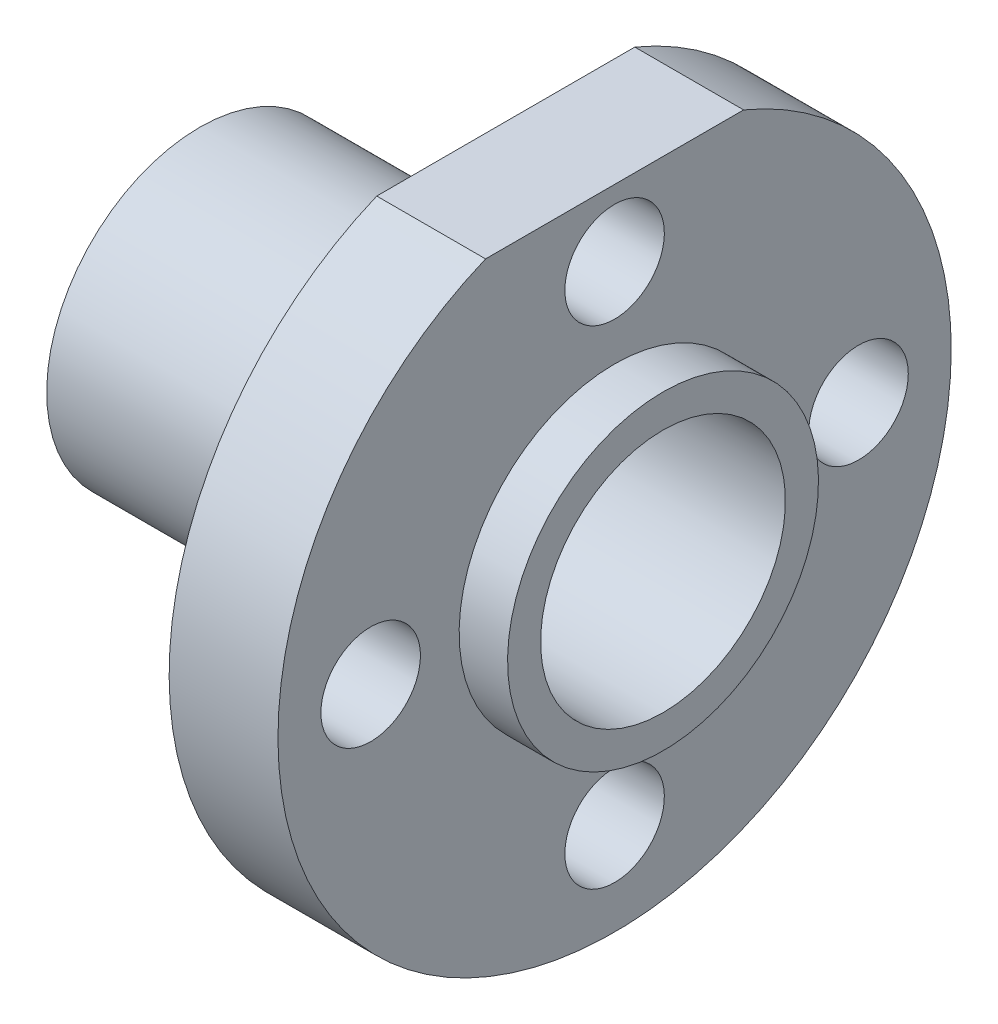
SolidWorks part; units mm, degrees
ref_plane "Front Plane" through (0, 0, 0) normal (0, 0, 1) x (1, 0, 0)
ref_plane "Top Plane" through (0, 0, 0) normal (0, 1, 0) x (1, 0, 0)
ref_plane "Right Plane" through (0, 0, 0) normal (1, 0, 0) x (0, 0, -1)
sketch "Sketch1" plane through (0, 0, 0) normal (0, 0, 1) x (1, 0, 0)
  line L0 (0, 0) -> (-15.1384, 0) construction
  line L2 (-15.1384, 5) -> (-5.1384, 5)
  line L3 (-5.1384, 5) -> (-5.1384, 11)
  line L9 (-5.1384, 11) -> (-1.5824, 11)
  line L10 (-1.5824, 11) -> (-1.5824, 5.08)
  line L11 (-1.5824, 5.08) -> (0, 5.08)
  line L12 (-15.1384, 5) -> (-15.1384, 4)
  line L13 (-15.1384, 4) -> (0, 4)
  line L14 (0, 4) -> (0, 5.08)
  dimension "D1" = 5
  dimension "D2" = 5.08
  dimension "D3" = 10
  dimension "D4" = 22
  dimension "D5" = 8
  dimension "D6" = 3.556
  dimension "D7" = 15.1384
revolve "Revolve1" add sketch "Sketch1" angle 360 about L0
sketch "Sketch2" plane through (-1.5824, 0, 0) normal (1, 0, 0) x (0, 0, -1)
  circle A0 centre (0, 7.971) radius 1.6256
  circle A1 centre (0, 0) radius 11 construction
  dimension "D1" = 3.2512
  dimension "D2" = 1.4034
extrude "Cut-Extrude1" cut sketch "Sketch2" against normal up to surface (3.556 mm away) up to face at (-5.1384, 5, 0)
pattern_circular "CirPattern1" count 4 over 360 about axis through (0, 0, 0) along (1, 0, 0) of "Cut-Extrude1"
sketch "Sketch3" plane through (-1.5824, 0, 0) normal (1, 0, 0) x (0, 0, -1)
  line L0 (-4.216, 10.16) -> (4.216, 10.16)
  circle A0 centre (0, 0) radius 11 construction
  arc A1 (4.216, 10.16) -> (-4.216, 10.16) centre (0, 0) ccw
  point P0 (0, 10.16)
  dimension "D1" = 10.16
extrude "Cut-Extrude2" cut sketch "Sketch3" against normal up to surface (3.556 mm away) up to face at (-5.1384, -1.6256, -7.971)
